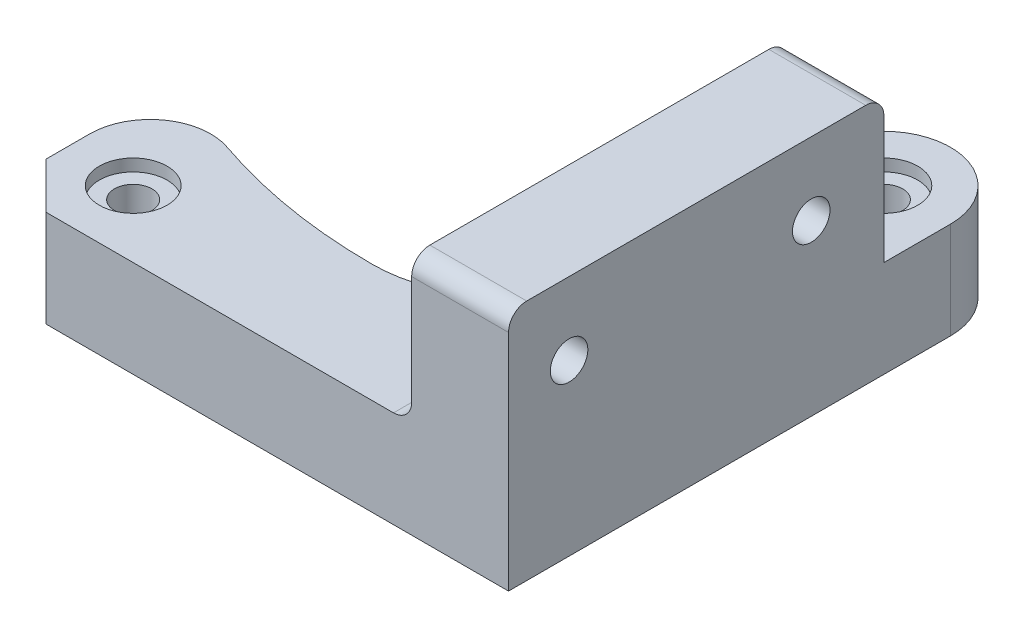
SolidWorks part; units mm, degrees
ref_plane "Alzado" through (0, 0, 0) normal (0, 0, 1) x (1, 0, 0)
ref_plane "Planta" through (0, 0, 0) normal (0, 1, 0) x (1, 0, 0)
ref_plane "Vista lateral" through (0, 0, 0) normal (1, 0, 0) x (0, 0, -1)
sketch "Croquis1" plane through (0, 0, 0) normal (0, 1, 0) x (1, 0, 0)
  line L0 (21, 42) -> (21, 0) construction
  line L1 (0, 0) -> (42, 0)
  line L2 (0, 0) -> (0, 42) construction
  line L3 (0, 42) -> (42, 42) construction
  line L4 (42, 0) -> (42, 36.5)
  line L5 (0, 15.0394) -> (0, 0)
  circle A0 centre (36.5, 36.5) radius 1.55
  circle A1 centre (5.5, 5.5) radius 1.55
  arc A2 (21, 9.75) -> (21, 32.25) centre (21, 21) ccw
  arc A3 (0, 15.0394) -> (21, 9.75) centre (20.9082, 53.7172) ccw
  arc A4 (42, 36.5) -> (31.1961, 37.9557) centre (36.5, 36.5) ccw
  arc A5 (21, 32.25) -> (31.1961, 37.9557) centre (20.567, 44.987) ccw
  dimension "D3" = 3.1
  dimension "D4" = 5.5
  dimension "D8" = 22.5
  dimension "D1" = 42
  dimension "D2" = 42
  dimension "D5" = 5.5
  dimension "D6" = 5.5
  dimension "D7" = 5.5
extrude "Saliente-Extruir2" add sketch "Croquis1" along normal blind 8
fillet "Redondeo1" radius 8 1 edges at (21, 4, -32.25)
fillet "Redondeo2" radius 5 1 edges at (0, 4, -15.0394)
sketch "Croquis2" plane through (0, 8, 0) normal (0, 1, 0) x (1, 0, 0)
  circle A0 centre (36.5, 36.5) radius 2.8
  circle A1 centre (5.5, 5.5) radius 2.8
  dimension "D1" = 5.6
extrude "Cortar-Extruir1" cut sketch "Croquis2" against normal blind 1
sketch "Croquis3" plane through (0, 8, 0) normal (0, 1, 0) x (1, 0, 0)
  line L1 (42, 0) -> (34, 0)
  line L2 (42, 0) -> (42, 31)
  line L3 (42, 31) -> (34, 31)
  line L4 (34, 0) -> (34, 31)
  dimension "D1" = 8
  dimension "D2" = 31
extrude "Saliente-Extruir3" add sketch "Croquis3" along normal blind 12
sketch "Croquis4" plane through (34, 0, 0) normal (-1, 0, 0) x (0, 0, 1)
  line L0 (-31, 14) -> (0, 14) construction
  line L1 (-31, 20) -> (-31, 8) construction
  line L2 (0, 20) -> (0, 8) construction
  circle A0 centre (-25, 14) radius 1.55
  circle A1 centre (-5, 14) radius 1.55
  dimension "D1" = 3.1
  dimension "D3" = 5
  dimension "D2" = 20
extrude "Cortar-Extruir2" cut sketch "Croquis4" against normal up to surface (8 mm away) up to face at (42, 9.3333, -22.5)
sketch "Croquis5" plane through (34, 0, 0) normal (-1, 0, 0) x (0, 0, 1)
  line L1 (-25, 17.3486) -> (-27.9, 15.6743)
  line L2 (-27.9, 15.6743) -> (-27.9, 12.3257)
  line L3 (-27.9, 12.3257) -> (-25, 10.6514)
  line L4 (-25, 10.6514) -> (-22.1, 12.3257)
  line L5 (-22.1, 12.3257) -> (-22.1, 15.6743)
  line L6 (-22.1, 15.6743) -> (-25, 17.3486)
  line L7 (-5, 17.3486) -> (-7.9, 15.6743)
  line L8 (-7.9, 15.6743) -> (-7.9, 12.3257)
  line L9 (-7.9, 12.3257) -> (-5, 10.6514)
  line L10 (-5, 10.6514) -> (-2.1, 12.3257)
  line L11 (-2.1, 12.3257) -> (-2.1, 15.6743)
  line L12 (-2.1, 15.6743) -> (-5, 17.3486)
  circle A0 centre (-25, 14) radius 2.9 construction
  circle A1 centre (-5, 14) radius 2.9 construction
  point P10 (-3.55, 11.4885)
  dimension "D1" = 5.8
  dimension "D2" = 5.8
extrude "Cortar-Extruir3" cut sketch "Croquis5" against normal blind 2.5 contours L1 L2 L3 L4 L5 L6 | L7 L8 L9 L10 L11 L12
fillet "Redondeo3" radius 1.5 1 edges at (34, 8, -15.5)
fillet "Redondeo4" radius 1.5 2 edges at (38, 20, 0) (38, 20, -31)
chamfer "Chaflán1" distance 3.8 angle 45 1 edges at (0, 4, 0)
